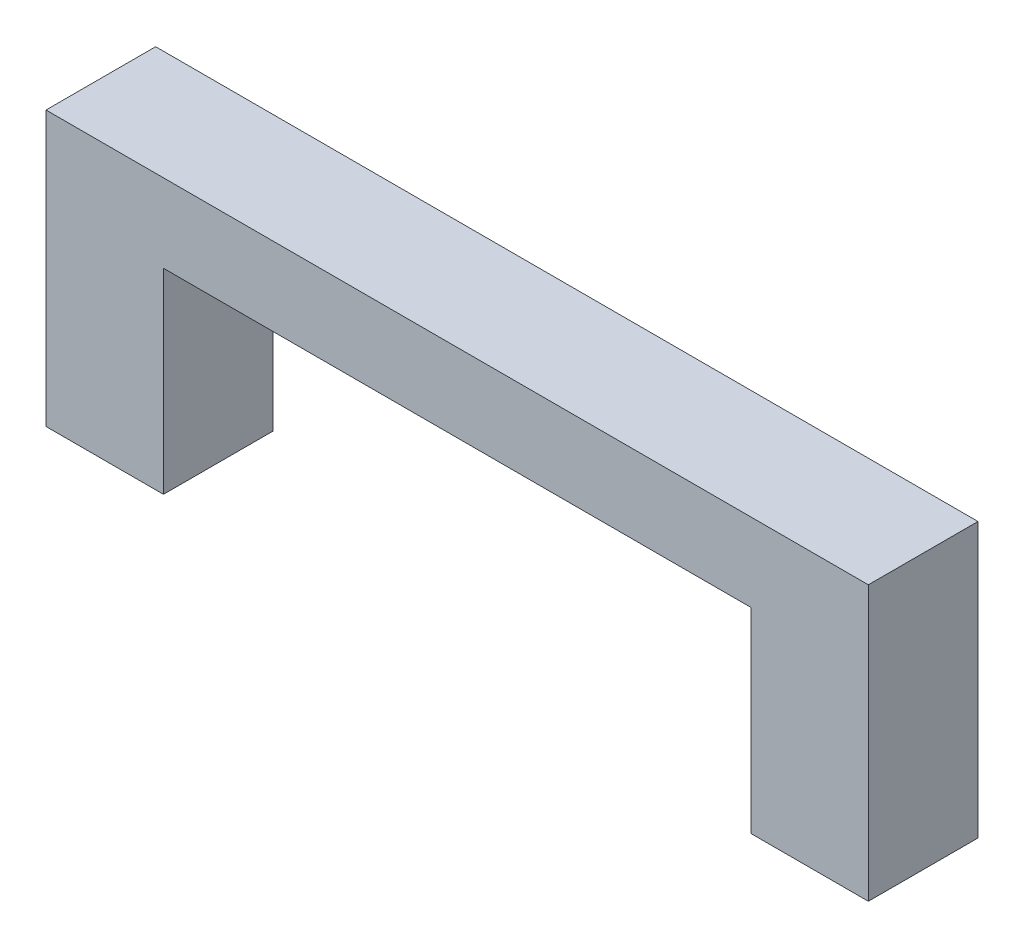
SolidWorks part; units mm, degrees
ref_plane "Front Plane" through (0, 0, 0) normal (0, 0, 1) x (1, 0, 0)
ref_plane "Top Plane" through (0, 0, 0) normal (0, 1, 0) x (1, 0, 0)
ref_plane "Right Plane" through (0, 0, 0) normal (1, 0, 0) x (0, 0, -1)
sketch "Sketch1" plane through (0, 0, 0) normal (0, 0, 1) x (1, 0, 0)
  line L0 (0, 0) -> (0, 7)
  line L1 (0, 7) -> (21, 7)
  line L2 (21, 7) -> (21, 0)
  line L3 (21, 0) -> (18, 0)
  line L4 (18, 0) -> (18, 5)
  line L5 (18, 5) -> (3, 5)
  line L6 (3, 5) -> (3, 0)
  line L7 (3, 0) -> (0, 0)
  point P9 (1.5, 0)
  point P10 (19.5, 0)
  dimension "D1" = 3
  dimension "D2" = 5
  dimension "D3" = 7
  dimension "D4" = 18
extrude "Boss-Extrude1" add sketch "Sketch1" along normal blind 2.8
sketch "Sketch2" plane through (0, 0, 0) normal (0, -1, 0) x (1, 0, 0)
  line L0 (3, 2.8) -> (3, 0) construction
  line L1 (0.5, 2.4) -> (2.5, 2.4)
  line L2 (0.5, 2.4) -> (0.5, 0.4)
  line L3 (0.5, 0.4) -> (2.5, 0.4)
  line L4 (2.5, 2.4) -> (2.5, 0.4)
  line L5 (0.5, 2.4) -> (2.5, 0.4) construction
  line L6 (0.5, 0.4) -> (2.5, 2.4) construction
  line L7 (18.5, 2.4) -> (20.5, 2.4)
  line L8 (18.5, 2.4) -> (18.5, 0.4)
  line L9 (18.5, 0.4) -> (20.5, 0.4)
  line L10 (20.5, 2.4) -> (20.5, 0.4)
  line L11 (18.5, 2.4) -> (20.5, 0.4) construction
  line L12 (18.5, 0.4) -> (20.5, 2.4) construction
  line L13 (0, 2.8) -> (3, 2.8) construction
  line L14 (21, 2.8) -> (21, 0) construction
  line L15 (18, 2.8) -> (21, 2.8) construction
  point P4 (1.5, 1.4)
  point P9 (19.5, 1.4)
  point P12 (3, 1.4)
  point P15 (1.5, 2.8)
  point P19 (21, 1.4)
  point P23 (19.5, 2.8)
  dimension "D1" = 2
extrude "Cut-Extrude1" cut sketch "Sketch2" against normal blind 2.2 contours L10 L7 L8 L9 | L1 L4 L3 L2
